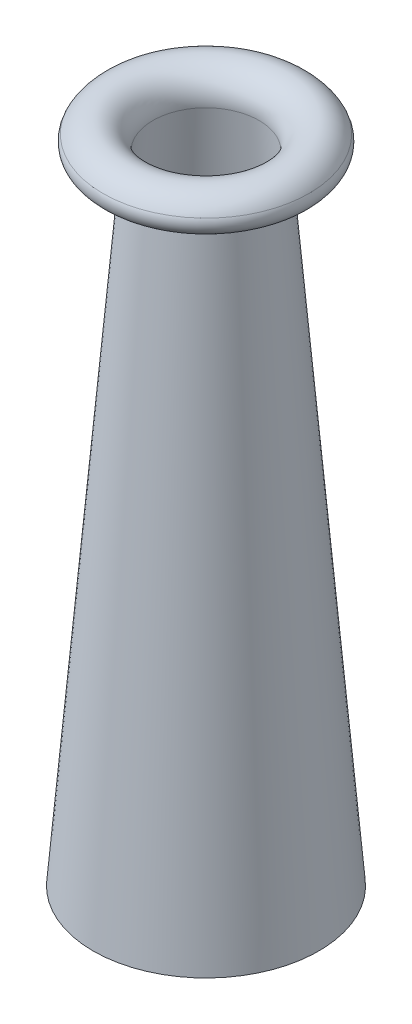
SolidWorks part; units mm, degrees
ref_plane "Front Plane" through (0, 0, 0) normal (0, 0, 1) x (1, 0, 0)
ref_plane "Top Plane" through (0, 0, 0) normal (0, 1, 0) x (1, 0, 0)
ref_plane "Right Plane" through (0, 0, 0) normal (1, 0, 0) x (0, 0, -1)
sketch "Sketch2" plane through (0, 0, 0) normal (0, 0, 1) x (1, 0, 0)
  line L0 (-12.7, 49.4064) -> (-25.4, -102.9936)
  line L1 (-14.2947, 49.5392) -> (-26.9947, -102.8608)
  line L2 (-20.5563, 51.0019) -> (-19.0466, 50.4714)
  line L3 (-26.9947, -102.8608) -> (-25.4, -102.9936)
  line L4 (0, 76.2622) -> (0, -115.8412) construction
  arc A0 (-12.7, 49.4064) -> (-24.6495, 52.9386) centre (-19.0406, 49.9347) ccw
  arc A1 (-24.6495, 52.9386) -> (-19.0466, 50.4714) centre (-21.9431, 51.4892) ccw
  arc A3 (-23.2388, 52.1831) -> (-20.5563, 51.0019) centre (-21.9431, 51.4892) ccw
  arc A4 (-14.2947, 49.5392) -> (-23.2388, 52.1831) centre (-19.0406, 49.9347) ccw
  dimension "D3" = 12.7
  dimension "D1" = 152.4
  dimension "D4" = 12.7
  dimension "D2" = 1.6002
revolve "Revolve1" add sketch "Sketch2" angle 360 about L4
